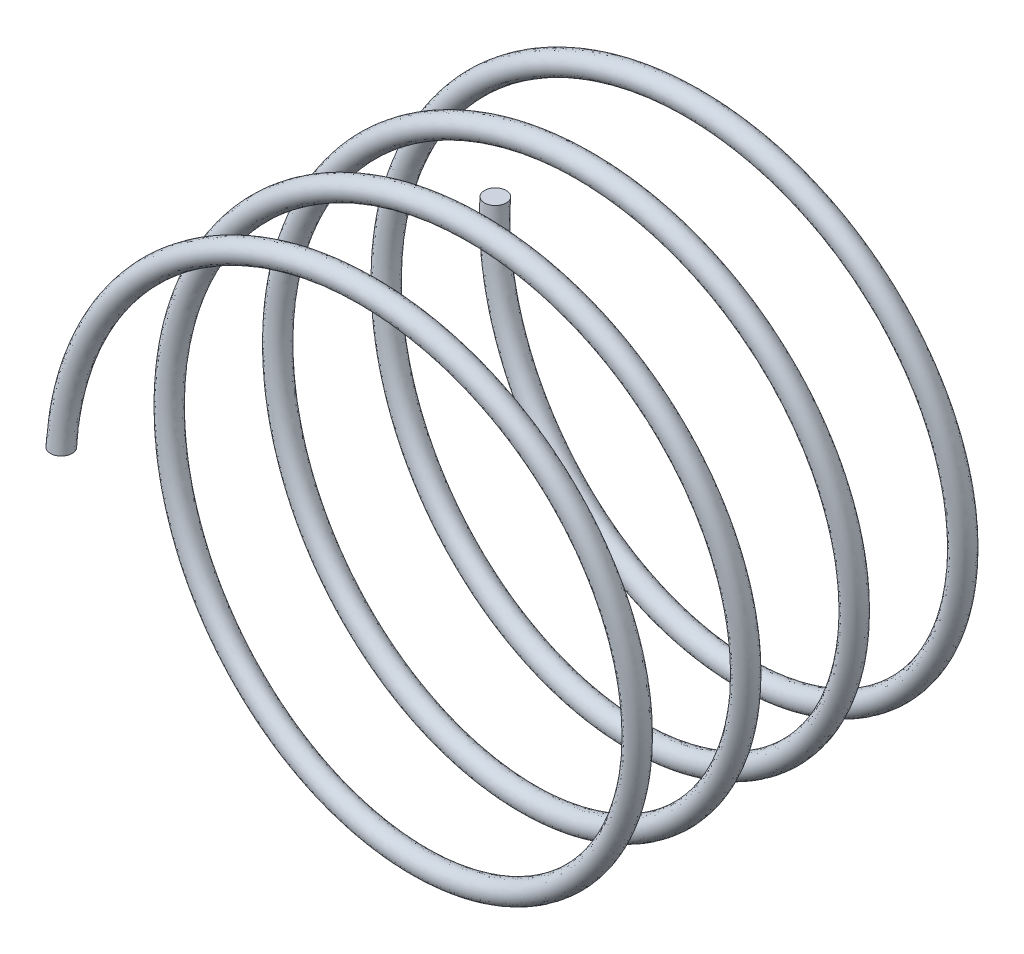
SolidWorks part; units mm, degrees
ref_plane "Front Plane" through (0, 0, 0) normal (0, 0, 1) x (1, 0, 0)
ref_plane "Top Plane" through (0, 0, 0) normal (0, 1, 0) x (1, 0, 0)
ref_plane "Right Plane" through (0, 0, 0) normal (1, 0, 0) x (0, 0, -1)
sketch "Sketch1" plane through (0, 0, 0) normal (0, 0, 1) x (1, 0, 0)
  circle A1 centre (0, 0) radius 60
  dimension "D1" = 120
curve "Helix/Spiral1" pitch 25 height 100 turns 4
sketch "Sketch3" plane through (0, 0, 0) normal (0, 1, 0) x (1, 0, 0)
  circle A0 centre (-60.0231, 0) radius 2.5
  dimension "D1" = 5
sweep "Sweep1" add profiles "Sketch3" path "Helix/Spiral1"
